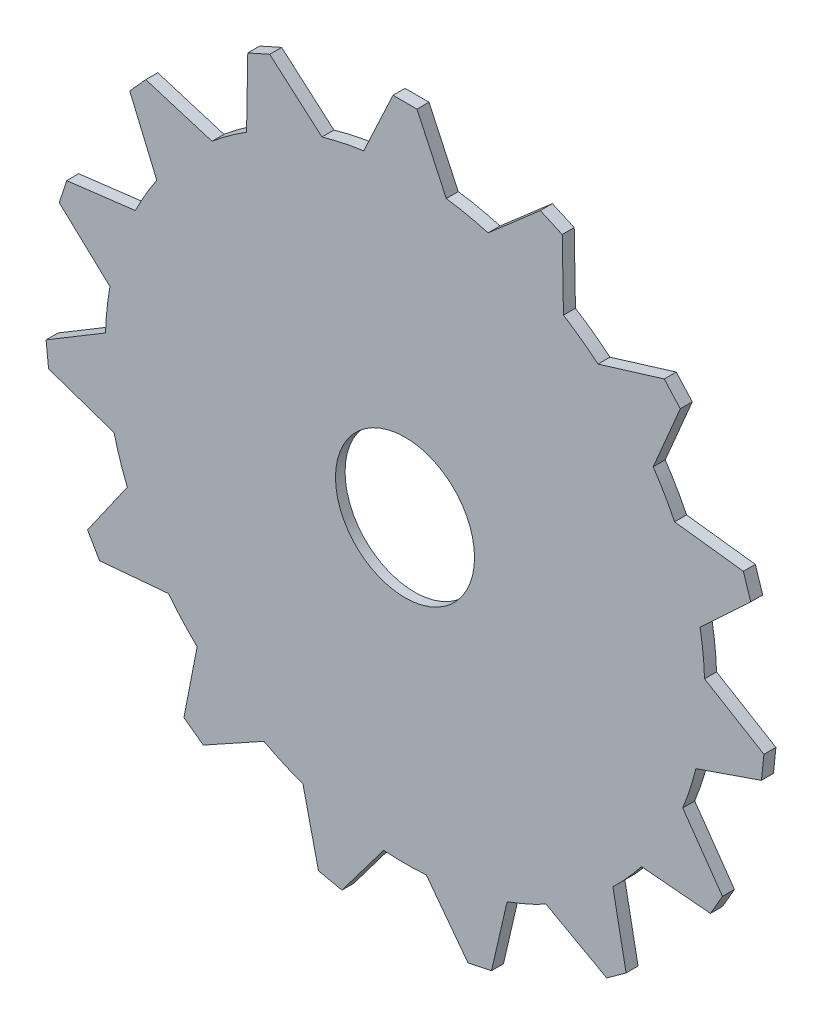
SolidWorks part; units mm, degrees
ref_plane "Front Plane" through (0, 0, 0) normal (0, 0, 1) x (1, 0, 0)
ref_plane "Top Plane" through (0, 0, 0) normal (0, 1, 0) x (1, 0, 0)
ref_plane "Right Plane" through (0, 0, 0) normal (1, 0, 0) x (0, 0, -1)
sketch "Sketch1" plane through (0, 0, 0) normal (0, 0, 1) x (1, 0, 0)
  circle A0 centre (0, 0) radius 31.75
  dimension "D1" = 63.5
extrude "Boss-Extrude1" add sketch "Sketch1" along normal blind 1.27
sketch "Sketch2" plane through (0, 0, 1.27) normal (0, 0, 1) x (1, 0, 0)
  line L0 (0, 31.75) -> (0, 38.1) construction
  line L1 (-1.27, 38.1) -> (1.27, 38.1)
  line L2 (1.27, 38.1) -> (4.3721, 31.4475)
  line L3 (-1.27, 38.1) -> (-4.3721, 31.4475)
  line L4 (70, -22.38) -> (63.3475, -19.2779)
  line L5 (70, -22.38) -> (70, -24.92)
  line L6 (70, -24.92) -> (63.3475, -28.0221)
  line L7 (9.52, -93.65) -> (12.6221, -86.9975)
  line L8 (9.52, -93.65) -> (6.98, -93.65)
  line L9 (6.98, -93.65) -> (3.8779, -86.9975)
  line L10 (-61.75, -33.17) -> (-55.0975, -36.2721)
  line L11 (-61.75, -33.17) -> (-61.75, -30.63)
  line L12 (-61.75, -30.63) -> (-55.0975, -27.5279)
  circle A0 centre (0, 0) radius 31.75 construction
  arc A1 (4.3721, 31.4475) -> (-4.3721, 31.4475) centre (0, 0) ccw
  point P25 (4.125, -27.775)
  circle M1 centre (0, 0) radius 31.75
  dimension "D1" = 1.27
  dimension "D2" = 4
  dimension "D3" = 6.35
  dimension "D4" = 65
extrude "Boss-Extrude2" add sketch "Sketch2" against normal blind 1.27 contours L12 L11 L10 M1 | A1 L0 L1 L3 | L0 L2 L1 M1 | L6 L5 L4 M1 | L9 L8 L7 M1
sketch "Sketch3" plane through (0, 0, 0) normal (0, 0, -1) x (-1, 0, 0)
  circle A0 centre (0, 0) radius 7.366
  dimension "D1" = 14.732
extrude "Cut-Extrude1" cut sketch "Sketch3" against normal blind 10
pattern_circular "CirPattern1" count 15 every 24 about axis through (0, 0, 0) along (0, 0, 1) of "Boss-Extrude2"
sketch "Sketch4" plane through (0, 0, 0) normal (0, 0, -1) x (-1, 0, 0)
  circle A0 centre (0, 0) radius 25.4
  dimension "D1" = 50.8
extrude "Cut-Extrude2" cut sketch "Sketch4" against normal blind 0.254
